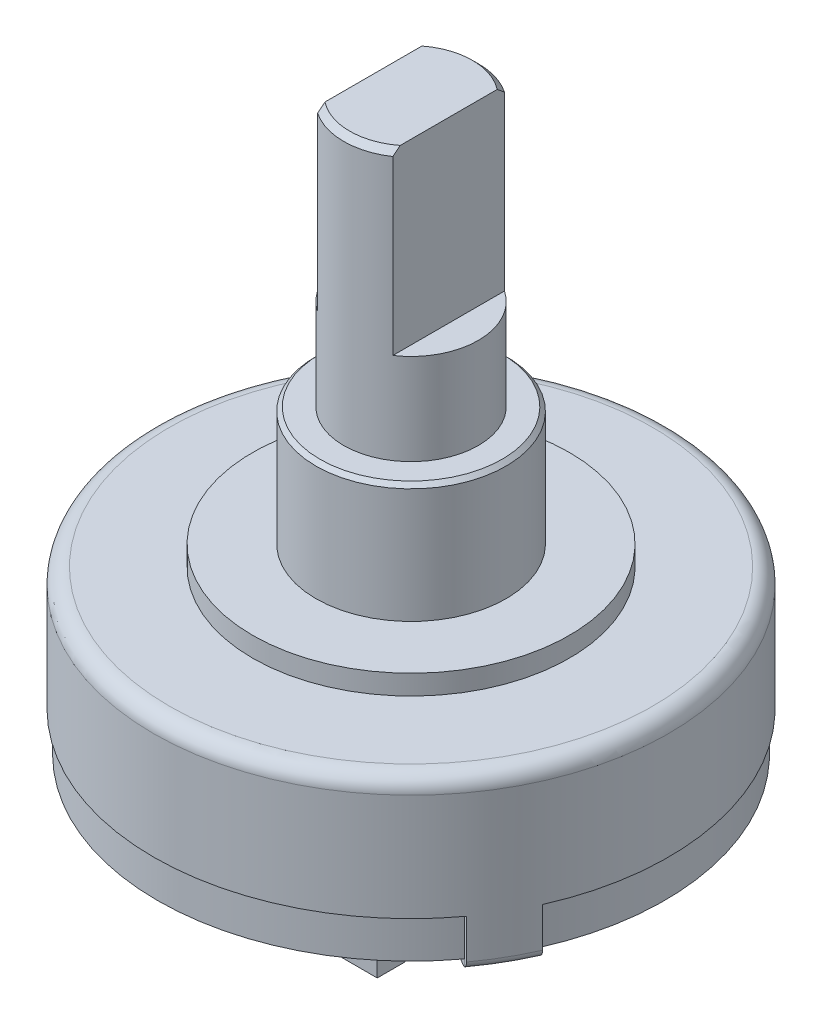
SolidWorks part; units mm, degrees
ref_plane "Front Plane" through (0, 0, 0) normal (0, 0, 1) x (1, 0, 0)
ref_plane "Top Plane" through (0, 0, 0) normal (0, 1, 0) x (1, 0, 0)
ref_plane "Right Plane" through (0, 0, 0) normal (1, 0, 0) x (0, 0, -1)
sketch "Sketch1" plane through (0, 0, 0) normal (0, 1, 0) x (1, 0, 0)
  circle A0 centre (0, 0) radius 6.5
extrude "Boss-Extrude1" add sketch "Sketch1" along normal blind 3.1
sketch "Sketch2" plane through (0, 3.1, 0) normal (0, 1, 0) x (1, 0, 0)
  circle A0 centre (0, 0) radius 4
extrude "Boss-Extrude2" add sketch "Sketch2" along normal blind 0.5
sketch "Sketch3" plane through (0, 3.6, 0) normal (0, 1, 0) x (-1, 0, 0)
  circle A0 centre (0, 0) radius 2.4
extrude "Boss-Extrude3" add sketch "Sketch3" along normal blind 3
sketch "Sketch4" plane through (0, 6.6, 0) normal (0, 1, 0) x (1, 0, 0)
  circle A0 centre (0, 0) radius 1.7
extrude "Boss-Extrude4" add sketch "Sketch4" along normal blind 6.8
chamfer "Chamfer1" distance 0.15 angle 45 1 edges at (0, 13.4, 1.7)
sketch "Sketch5" plane through (0, 13.4, 0) normal (0, 1, 0) x (1, 0, 0)
  line L0 (0, 0) -> (0.95, 0) construction
  line L1 (0, 0) -> (-0.95, 0) construction
  line L2 (0.95, 0) -> (0.95, 1.9535)
  line L3 (0.95, 1.9535) -> (2.2916, 1.9535)
  line L4 (2.2916, 1.9535) -> (2.2916, -1.887)
  line L5 (2.2916, -1.887) -> (0.95, -1.887)
  line L6 (0.95, -1.887) -> (0.95, 0)
  line L7 (-0.95, 0) -> (-0.95, 2.0557)
  line L8 (-0.95, 2.0557) -> (-2.2844, 2.0557)
  line L9 (-2.2844, 2.0557) -> (-2.2129, -1.8155)
  line L10 (-2.2129, -1.8155) -> (-0.95, -1.8155)
  line L11 (-0.95, -1.8155) -> (-0.95, 0)
  dimension "D1" = 0.95
  dimension "D2" = 0.95
extrude "Cut-Extrude1" cut sketch "Sketch5" against normal blind 4.5
sketch "Sketch6" plane through (0, 0, 0) normal (0, -1, 0) x (1, 0, 0)
  circle A0 centre (0, 0) radius 6.4
extrude "Boss-Extrude5" add sketch "Sketch6" along normal blind 1
fillet "Fillet1" radius 0.4 1 edges at (0, 3.1, 6.5)
chamfer "Chamfer2" distance 0.1 angle 45 1 edges at (0, 6.6, 2.4)
sketch "Sketch7" plane through (0, 0, 0) normal (0, -1, 0) x (1, 0, 0)
  line L0 (0, 0) -> (-5.6292, 3.25) construction
  line L1 (0, 0) -> (0, -6.5) construction
  line L2 (0, 0) -> (5.6292, 3.25) construction
  line L3 (5.6292, 3.25) -> (5.2792, 3.8562) construction
  line L4 (5.6292, 3.25) -> (5.9792, 2.6438) construction
  line L5 (5.1515, 3.7976) -> (5.2421, 3.8432)
  line L6 (5.8543, 2.5861) -> (5.9456, 2.6267)
  line L7 (-5.6292, 3.25) -> (-5.2792, 3.8562) construction
  line L8 (-5.6292, 3.25) -> (-5.9792, 2.6438) construction
  line L9 (-5.2421, 3.8432) -> (-5.1515, 3.7976)
  line L10 (-5.8543, 2.5861) -> (-5.9456, 2.6267)
  line L11 (0, -6.5) -> (0.7, -6.5) construction
  line L12 (0.7, -6.5) -> (0, -6.5) construction
  line L13 (0, -6.5) -> (-0.7, -6.5) construction
  line L14 (-0.7, -6.4622) -> (-0.6886, -6.3628)
  line L15 (0.7, -6.4622) -> (0.6819, -6.3636)
  line L16 (5.1515, 3.7976) -> (5.8543, 2.5861)
  line L17 (-5.1515, 3.7976) -> (-5.8543, 2.5861)
  line L18 (-0.6886, -6.3628) -> (0.6819, -6.3636)
  circle A0 centre (0, 0) radius 6.5 construction
  circle A3 centre (0, 0) radius 6.5
  arc A4 (5.9456, 2.6267) -> (5.2421, 3.8432) centre (0, 0) ccw
  arc A9 (-5.2421, 3.8432) -> (-5.9456, 2.6267) centre (0, 0) ccw
  arc A13 (-0.7, -6.4622) -> (0.7, -6.4622) centre (0, 0) ccw
  dimension "D1" = 120
  dimension "D2" = 120
  dimension "D3" = 0
extrude "Boss-Extrude6" add sketch "Sketch7" along normal blind 1.2
sketch "Sketch8" plane through (5.5029, 0, 3.1918) normal (-0.865, 0, -0.5017) x (-0.5017, 0, 0.865)
  line L0 (0.7003, -1.2) -> (0.7003, -1)
  line L1 (0.7003, -1) -> (-0.7003, -1)
  line L2 (-0.7003, -1) -> (-0.7003, -1.2)
  line L3 (-0.7003, -1.2) -> (0.7003, -1.2)
extrude "Boss-Extrude7" add sketch "Sketch8" along normal blind 1.2
sketch "Sketch9" plane through (-5.5029, 0, 3.1918) normal (0.865, 0, -0.5017) x (-0.5017, 0, -0.865)
  line L0 (-0.7003, -1) -> (-0.7003, -1.2)
  line L1 (-0.7003, -1.2) -> (0.7003, -1.2)
  line L2 (0.7003, -1.2) -> (0.7003, -1)
  line L3 (0.7003, -1) -> (-0.7003, -1)
extrude "Boss-Extrude8" add sketch "Sketch9" along normal blind 1.2
sketch "Sketch10" plane through (-0.0034, 0, -6.3632) normal (0.0005, 0, 1) x (1, 0, -0.0005)
  line L0 (0.6853, -1.2) -> (0.6853, -1)
  line L1 (0.6853, -1) -> (-0.6853, -1)
  line L2 (-0.6853, -1) -> (-0.6853, -1.2)
  line L3 (-0.6853, -1.2) -> (0.6853, -1.2)
extrude "Boss-Extrude9" add sketch "Sketch10" along normal blind 1.2
fillet "Fillet2" radius 0.5 6 edges at (-4.1135, -1.1, 3.1955) (-4.8162, -1.1, 1.984) (4.8162, -1.1, 1.984) (4.1135, -1.1, 3.1955) (0.6825, -1.1, -5.1636) (-0.688, -1.1, -5.1628)
fillet "Fillet3" radius 0.2 3 edges at (5.6269, -1.2, 3.254) (0, -1.2, -6.5) (-5.6269, -1.2, 3.254)
sketch "Sketch11" plane through (0, -1, 0) normal (0, -1, 0) x (1, 0, 0)
  line L1 (-0.6001, 1.4964) -> (0.4977, 1.4964)
  line L2 (-0.6001, 1.4964) -> (-0.6001, 2.2628)
  line L3 (-0.6001, 2.2628) -> (0.4977, 2.2628)
  line L4 (0.4977, 1.4964) -> (0.4977, 2.2628)
  line L5 (-0.6001, 1.4964) -> (0.4977, 2.2628) construction
  line L6 (-0.6001, 2.2628) -> (0.4977, 1.4964) construction
  line L7 (1.4299, 2.615) -> (2.4656, 2.615)
  line L8 (1.4299, 2.615) -> (1.4299, 3.3192)
  line L9 (1.4299, 3.3192) -> (2.4656, 3.3192)
  line L10 (2.4656, 2.615) -> (2.4656, 3.3192)
  line L11 (1.4299, 2.615) -> (2.4656, 3.3192) construction
  line L12 (1.4299, 3.3192) -> (2.4656, 2.615) construction
  line L13 (-1.8844, 2.615) -> (-3.1272, 2.615)
  line L14 (-1.8844, 2.615) -> (-1.8844, 3.3192)
  line L15 (-1.8844, 3.3192) -> (-3.1272, 3.3192)
  line L16 (-3.1272, 2.615) -> (-3.1272, 3.3192)
  line L17 (-1.8844, 2.615) -> (-3.1272, 3.3192) construction
  line L18 (-1.8844, 3.3192) -> (-3.1272, 2.615) construction
  point P0 (-0.0512, 1.8796)
  point P5 (1.9477, 2.9671)
  point P10 (-2.5058, 2.9671)
extrude "Boss-Extrude10" add sketch "Sketch11" along normal blind 2
